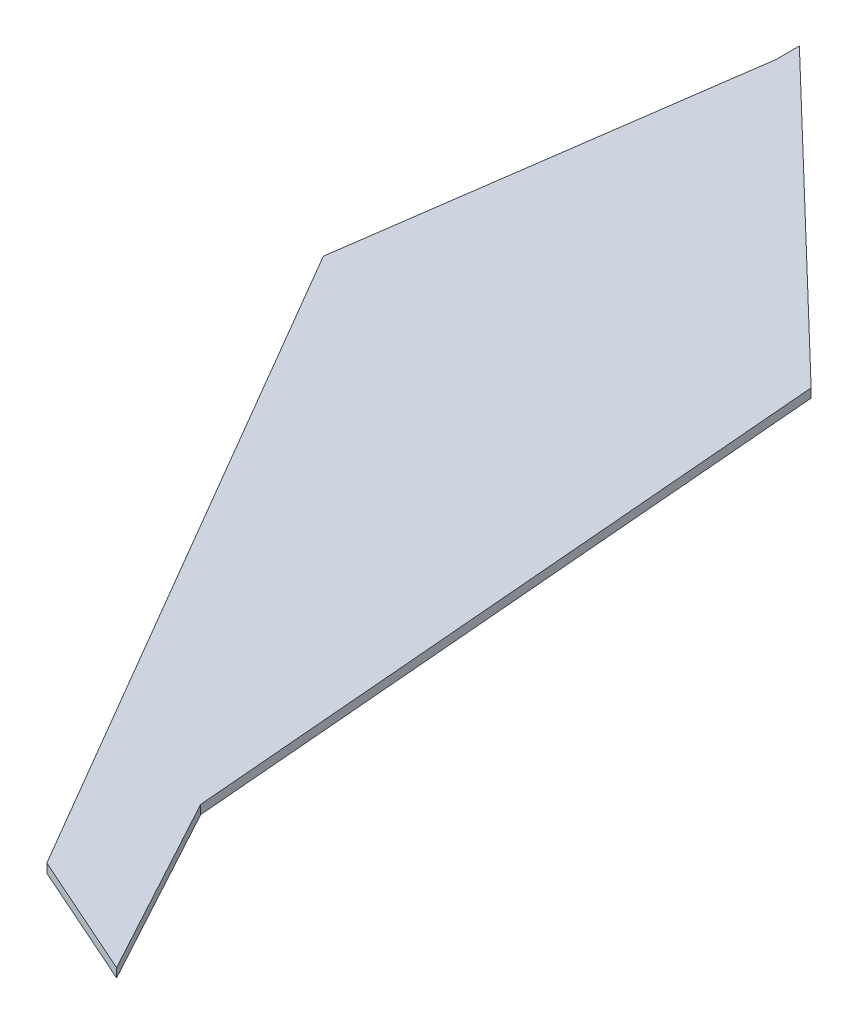
SolidWorks part; units mm, degrees
ref_plane "Plan de face" through (0, 0, 0) normal (0, 0, 1) x (1, 0, 0)
ref_plane "Plan de dessus" through (0, 0, 0) normal (0, 1, 0) x (1, 0, 0)
ref_plane "Plan de droite" through (0, 0, 0) normal (1, 0, 0) x (0, 0, -1)
sketch "Esquisse1" plane through (0, 0, 0) normal (0, 1, 0) x (1, 0, 0)
  line L0 (-6.5854, 178.1422) -> (-74.3565, 243.2747)
  line L1 (-74.3565, 243.2747) -> (-74.3565, 237.9788)
  line L2 (-74.3565, 237.9788) -> (-86.9239, 148.9895)
  line L3 (-86.9239, 148.9895) -> (0, 0)
  line L4 (0, 0) -> (28.1915, -12.5465)
  line L5 (28.1915, -12.5465) -> (5.8771, 28.6445)
  line L6 (5.8771, 28.6445) -> (-6.5854, 178.1422)
  point P7 (0, 0)
extrude "Boss.-Extru.1" add sketch "Esquisse1" along normal blind 2
